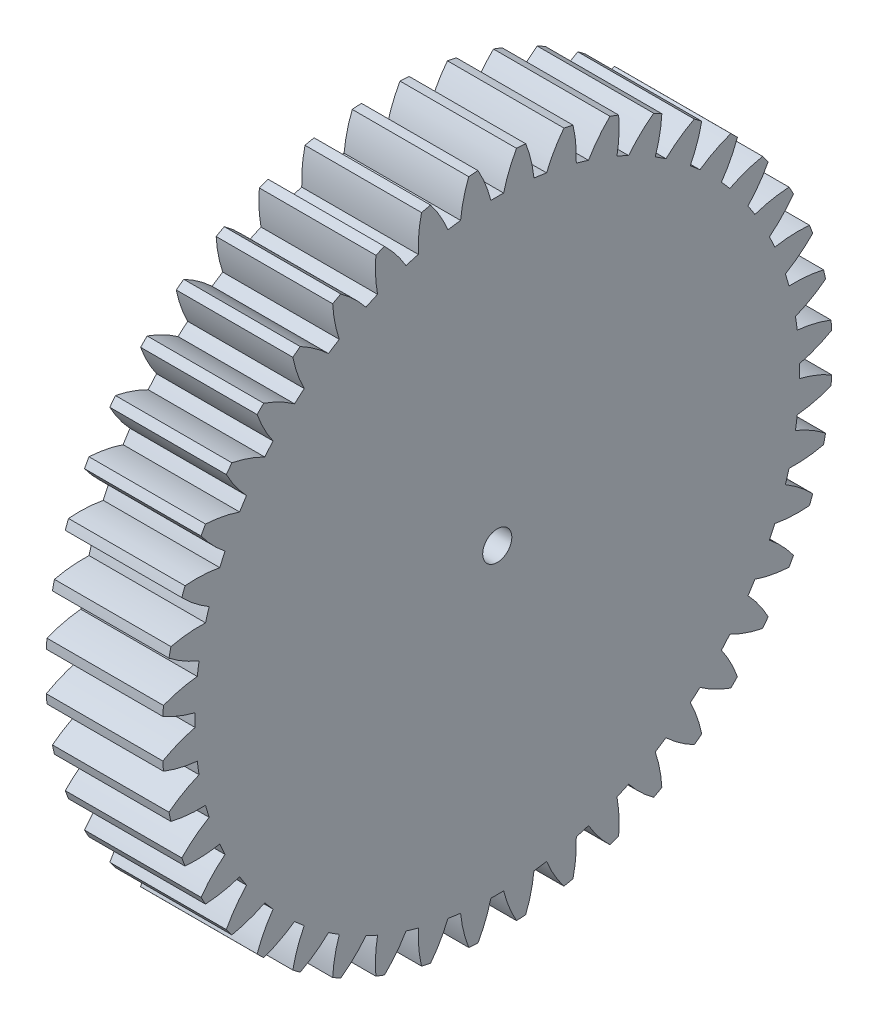
SolidWorks part; units mm, degrees
ref_plane "Plane1" through (0, 0, 0) normal (0, 0, 1) x (1, 0, 0)
ref_plane "Plane2" through (0, 0, 0) normal (0, 1, 0) x (1, 0, 0)
ref_plane "Plane3" through (0, 0, 0) normal (1, 0, 0) x (0, 0, -1)
sketch "HoldingSke" plane through (0, 0, 0) normal (0, 1, 0) x (1, 0, 0)
  line L0 (0, 0) -> (0.2877, -0.2779)
  line L1 (-15, 0) -> (100, 0) construction
  line L2 (0, 0) -> (-2.1039, 2.3779)
  line L3 (0, 0) -> (-11.863, 4.5341)
  line L4 (0, 0) -> (6.2122, 5.9991)
  line L5 (0, 0) -> (-46.8476, -17.4728)
  line L6 (0, 0) -> (-16.5793, -11.1861)
  line L7 (-2.1039, 2.3779) -> (8.6586, 51.2059)
  line L8 (-76.2, 54.61) -> (-75.3, 54.61)
  line L9 (-71.009, 38.7566) -> (-53.1078, 45.2721)
  line L10 (-76.2, 71.12) -> (104.1128, 71.12)
  line L11 (0, 0) -> (-20, 0)
  line L12 (-76.2, 101.6) -> (-76.113, 101.6)
  line L13 (24.9733, 27.94) -> (52.9518, 28.4284)
  line L14 (24.9733, 27.94) -> (24.9743, 27.94)
  line L15 (24.9733, 27.94) -> (100.4006, 29.5858)
  line L16 (-63.627, -2.5) -> (-12.827, -2.5)
  circle A0 centre (0, 0) radius 2.5
  circle A1 centre (0, 0) radius 37.5
  circle A2 centre (0, 0) radius 37.5
  circle A3 centre (0, 0) radius 2.5
  dimension "MHD" = 75
  dimension "Hub_dia" = 75
  dimension "Bore" = 5
  dimension "MBD" = 5
  dimension "Num_teeth" = 44
  dimension "Pitch" = 0.4
  dimension "Overall_len" = 50
  dimension "Show_teeth" = 44
  dimension "Thickness" = 20
  dimension "OAL" = 50.0001
  dimension "T_dim" = 0.9
  dimension "Ap" = 20
  dimension "H" = 19.05
  dimension "Pitch_radius" = 180.3128
  dimension "Width" = 20
  dimension "Backlash" = 0.087
  dimension "Addendum_fac" = 1
  dimension "Dedendum_fac" = 1.25
  dimension "Clearance_fac" = 0.25
  dimension "Dedendum_add" = 0.001
  dimension "Module" = 2.5
sketch "BasProSke" plane through (0, 0, 0) normal (0, 1, 0) x (1, 0, 0)
  line L0 (-10, 0) -> (60, 0) construction
  line L1 (0, 0) -> (0, 57.5)
  line L2 (0, 0) -> (20, 0)
  line L3 (20, 0) -> (20, 57.5)
  line L4 (20, 57.5) -> (0, 57.5)
  dimension "Thickness" = 20
  dimension "Diameter" = 115
revolve "Base-Revolve" add sketch "BasProSke" angle 360 about L0
sketch "TooCutSke" plane through (0, 0, 0) normal (1, 0, 0) x (0, 0, -1)
  line L1 (0, 0) -> (0, 107) construction
  line L2 (0, 0) -> (-2.1153, 54.9593) construction
  line L3 (0, 0) -> (-7.8431, 109.6602) construction
  line L4 (-2.1153, 54.9593) -> (-3.9215, 54.8301) construction
  arc A0 (1.0964, 51.8624) -> (-1.0964, 51.8624) centre (0, 0) ccw
  arc A1 (3.3223, 57.4294) -> (-3.3223, 57.4294) centre (0, 0) ccw
  circle A2 centre (0, 0) radius 55 construction
  circle A3 centre (0, 0) radius 51.6831 construction
  arc A4 (-1.0964, 51.8624) -> (-3.3223, 57.4294) centre (-22.4465, 46.5543) ccw
  arc A5 (3.3223, 57.4294) -> (1.0964, 51.8624) centre (22.4465, 46.5543) ccw
  dimension "Root_dia" = 103.748
  dimension "Overcut_dia" = 115.0508
  dimension "Pitch_dia" = 110
  dimension "Base_dia" = 103.3662
  dimension "Flank_rad" = 22
  dimension "Half_ang" = 4.091
  dimension "Half_CT" = 1.8108
extrude "ToothCut" cut sketch "TooCutSke" along normal through all
fillet "Breaks" [suppressed] radius 0.05
fillet "RootFillets" [suppressed] radius 0.626
pattern_circular "TeethCuts" count 44 every 8.182 about axis through (-10, 0, 0) along (1, 0, 0) of "ToothCut", "RootFillets", "Breaks"
sketch "HubNeaOneSke" plane through (0, 0, 0) normal (-1, 0, 0) x (0, 0, 1)
  circle A0 centre (0, 0) radius 37.5
  dimension "Diameter" = 75
extrude "HubNearOne" [suppressed] add sketch "HubNeaOneSke" along normal blind 30.0001
sketch "HubNeaBotSke" plane through (0, 0, 0) normal (-1, 0, 0) x (0, 0, 1)
  circle A0 centre (0, 0) radius 37.5
  dimension "Diameter" = 75
extrude "HubNearBoth" [suppressed] add sketch "HubNeaBotSke" along normal blind 15
ref_plane "FarPln" through (20, 0, 0) normal (1, 0, 0) x (0, 0, -1)
sketch "HubFarSke" plane through (20, 0, 0) normal (1, 0, 0) x (0, 0, -1)
  circle A0 centre (0, 0) radius 37.5
  dimension "Diameter" = 75
extrude "HubFar" [suppressed] add sketch "HubFarSke" along normal blind 15
sketch "BorSke" plane through (0, 0, 0) normal (1, 0, 0) x (0, 0, -1)
  circle A0 centre (0, 0) radius 2.5
  dimension "Diameter" = 5
extrude "Bore" cut sketch "BorSke" along normal mid plane 100.0001
sketch "KeySke" plane through (0, 0, 0) normal (1, 0, 0) x (0, 0, -1)
  line L0 (-1, 0) -> (-1, 3.4)
  line L1 (-1, 3.4) -> (1, 3.4)
  line L2 (1, 3.4) -> (1, 0)
  line L3 (0, 0) -> (0, 34) construction
  line L4 (-1, 0) -> (1, 0)
  dimension "Offset" = 3.4
extrude "Keyway" [suppressed] cut sketch "KeySke" along normal mid plane 100.0001
pattern_circular "Keyway2" [suppressed] count 2 every 90 about axis through (-10, 0, 0) along (1, 0, 0)
equation "' \"Module@HoldingSke\" = 6.35"
equation "' \"Num_teeth@HoldingSke\" = 12"
equation "' \"Ap@HoldingSke\" =  20"
equation "' \"Ap@HoldingSke\" = 20"
equation "' \"Width@HoldingSke\" = 0.5 * 25.4"
equation "' \"Hub_dia@HoldingSke\"= 1 * 25.4"
equation "' \"Hub_dia@HoldingSke\" = 1 * 25.4"
equation "' \"Overall_len@HoldingSke\" = 1.0 * 25.4"
equation "' \"Bore@HoldingSke\" = 0.75 * 25.4"
equation "' \"T_dim@HoldingSke\" = 0.1 * 25.4"
equation "' \"Width@KeySke\" = 0.25 * 25.4"
equation "' \"Show_teeth@HoldingSke\" = 13"
equation "' \"Backlash@HoldingSke\" = 0.009 * 25.4"
equation "' \"Addendum_fac@HoldingSke\" = 1.0"
equation "' \"Dedendum_fac@HoldingSke\" = 1.25"
equation "' \"Dedendum_add@HoldingSke\" = 0.00005 * 25.4"
equation "' \"Clearance_fac@HoldingSke\" = 0.25"
equation "\"Pitch@HoldingSke\" = 1 / \"Module@HoldingSke\""
equation "\"Overcut_dia@TooCutSke\" = (\"Num_teeth@HoldingSke\" + 2 * \"Addendum_fac@HoldingSke\") / \"Pitch@HoldingSke\" + 0.002 * 25.4"
equation "\"Pitch_dia@TooCutSke\" = \"Num_teeth@HoldingSke\" / \"Pitch@HoldingSke\""
equation "\"Base_dia@TooCutSke\" = \"Num_teeth@HoldingSke\" / \"Pitch@HoldingSke\" * cos((\"Ap@HoldingSke\"  * 3.14159265 / 180))"
equation "\"Root_dia@TooCutSke\" = (\"Num_teeth@HoldingSke\" + 2) / \"Pitch@HoldingSke\" - 2 * (\"Addendum_fac@HoldingSke\" + \"Dedendum_fac@HoldingSke\") / \"Pitch@HoldingSke\" - \"Dedendum_add@HoldingSke\" * 2"
equation "\"Half_ang@TooCutSke\" = 180 / \"Num_teeth@HoldingSke\""
equation "\"Half_CT@TooCutSke\" = \"Num_teeth@HoldingSke\" / \"Pitch@HoldingSke\" * sin((3.14159265 / 2 / \"Num_teeth@HoldingSke\")) / 2 - 7 * \"Backlash@HoldingSke\" / 4"
equation "\"Flank_rad@TooCutSke\" = \"Num_teeth@HoldingSke\" / \"Pitch@HoldingSke\" / 5"
equation "\"Radius@RootFillets\" = \"Clearance_fac@HoldingSke\" / \"Pitch@HoldingSke\" + \"Dedendum_add@HoldingSke\""
equation "\"Break_rad@Breaks\" = 0.02 / \"Pitch@HoldingSke\""
equation "\"Thickness@HoldingSke\" = \"Width@HoldingSke\""
equation "\"OAL@HoldingSke\" = \"Thickness@HoldingSke\""
equation "\"MHD@HoldingSke\" = (\"Num_teeth@HoldingSke\" + 2) / \"Pitch@HoldingSke\" - 2 * (\"Addendum_fac@HoldingSke\" + \"Dedendum_fac@HoldingSke\")  / \"Pitch@HoldingSke\" - \"Dedendum_add@HoldingSke\" * 2"
equation "\"MBD@HoldingSke\" = (\"Num_teeth@HoldingSke\" + 2) / \"Pitch@HoldingSke\" - 2 * (\"Addendum_fac@HoldingSke\" + \"Dedendum_fac@HoldingSke\")  / \"Pitch@HoldingSke\" - \"Dedendum_add@HoldingSke\" * 2 - 0.002 * 25.4"
equation "\"MHD@HoldingSke\" = ((sgn( \"MHD@HoldingSke\" - \"Hub_dia@HoldingSke\" )-1)*( \"MHD@HoldingSke\" - \"Hub_dia@HoldingSke\" ))/-2+ \"Hub_dia@HoldingSke\""
equation "\"MBD@HoldingSke\" = ((sgn( \"MBD@HoldingSke\" - \"Bore@HoldingSke\" )-1)*( \"MBD@HoldingSke\" - \"Bore@HoldingSke\" ))/-2+ \"Bore@HoldingSke\""
equation "\"OAL@HoldingSke\" = ((sgn( \"OAL@HoldingSke\" - \"Overall_len@HoldingSke\" )+1)*( \"OAL@HoldingSke\" - \"Overall_len@HoldingSke\" ))/2 + \"Overall_len@HoldingSke\" + 0.000002 * 25.4"
equation "\"Num_teeth@TeethCuts\" = int( \"Show_teeth@HoldingSke\" ) + 1"
equation "\"Num_teeth@TeethCuts\" = ((sgn( \"Num_teeth@TeethCuts\" - \"Num_teeth@HoldingSke\" )-1)*( \"Num_teeth@TeethCuts\" - \"Num_teeth@HoldingSke\" ))/-2+ \"Num_teeth@HoldingSke\""
equation "\"Num_teeth@TeethCuts\" = ((sgn( \"Num_teeth@TeethCuts\" - 2.0)+1)*( \"Num_teeth@TeethCuts\" - 2.0))/2 +2.0"
equation "\"Angle@TeethCuts\" = 360.0 / \"Num_teeth@HoldingSke\""
equation "\"Diameter@BasProSke\" = (\"Num_teeth@HoldingSke\" + 2 * \"Addendum_fac@HoldingSke\") / \"Pitch@HoldingSke\""
equation "\"Thickness@BasProSke\"  = \"Thickness@HoldingSke\""
equation "' \"Fillet_rad@BasProSke\" =  \"Thickness@HoldingSke\" * 0.05"
equation "' \"Fillet_rad@BasProSke\" = \"Thickness@HoldingSke\" * 0.05"
equation "\"MHD@HoldingSke\" = ((sgn( \"MHD@HoldingSke\" - \"Root_dia@TooCutSke\" )-1)*( \"MHD@HoldingSke\" - \"Root_dia@TooCutSke\" ))/-2+ \"Root_dia@TooCutSke\""
equation "\"Diameter@HubNeaOneSke\" = \"MHD@HoldingSke\""
equation "\"Length@HubNearOne\" = \"OAL@HoldingSke\" - \"Thickness@BasProSke\""
equation "\"Diameter@HubNeaBotSke\" = \"MHD@HoldingSke\""
equation "\"Length@HubNearBoth\" = ( \"OAL@HoldingSke\" - \"Thickness@BasProSke\" ) / 2.0"
equation "\"Thickness@FarPln\" = \"Thickness@BasProSke\""
equation "\"Diameter@HubFarSke\" = \"MHD@HoldingSke\""
equation "\"Length@HubFar\" = ( \"OAL@HoldingSke\" - \"Thickness@BasProSke\" ) / 2.0"
equation "\"Diameter@BorSke\" = \"MBD@HoldingSke\""
equation "\"D1@Bore\" = \"OAL@HoldingSke\" * 2.0"
equation "\"D1@Keyway\" = \"OAL@HoldingSke\" * 2.0"
equation "\"Offset@KeySke\" = \"T_dim@HoldingSke\" + \"MBD@HoldingSke\" / 2.0"
